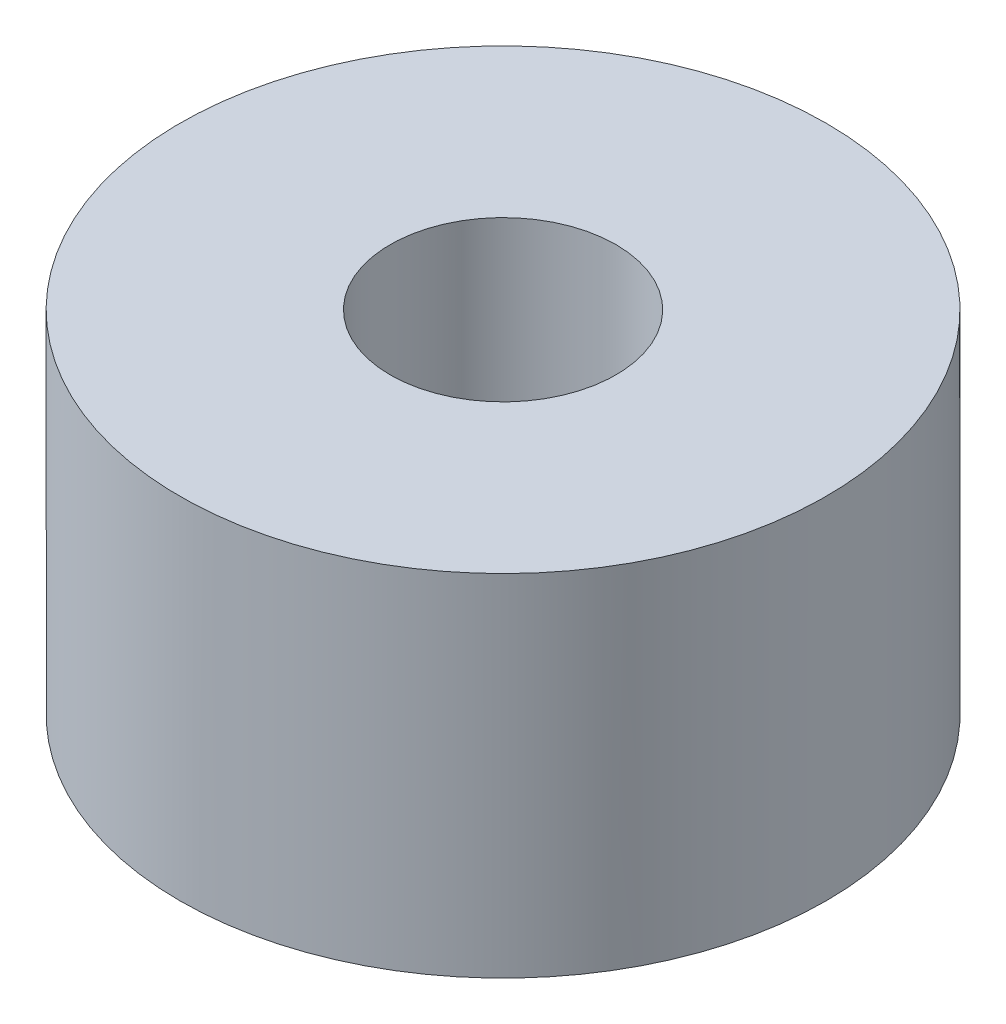
SolidWorks part; units mm, degrees
ref_plane "Front Plane" through (0, 0, 0) normal (0, 0, 1) x (1, 0, 0)
ref_plane "Top Plane" through (0, 0, 0) normal (0, 1, 0) x (1, 0, 0)
ref_plane "Right Plane" through (0, 0, 0) normal (1, 0, 0) x (0, 0, -1)
sketch "Sketch1" plane through (0, -39.4518, 0) normal (0, 1, 0) x (1, 0, 0)
  circle A0 centre (71.8117, 2.1472) radius 4.15
  circle A1 centre (71.8117, 2.1472) radius 4.25 construction
  circle A2 centre (71.8117, 2.1472) radius 1.45
  circle A3 centre (71.8117, 2.1472) radius 1.45 construction
  dimension "D1" = 0.1
extrude "Boss-Extrude1" add sketch "Sketch1" along normal offset from surface (4.5 mm away) 0.1
